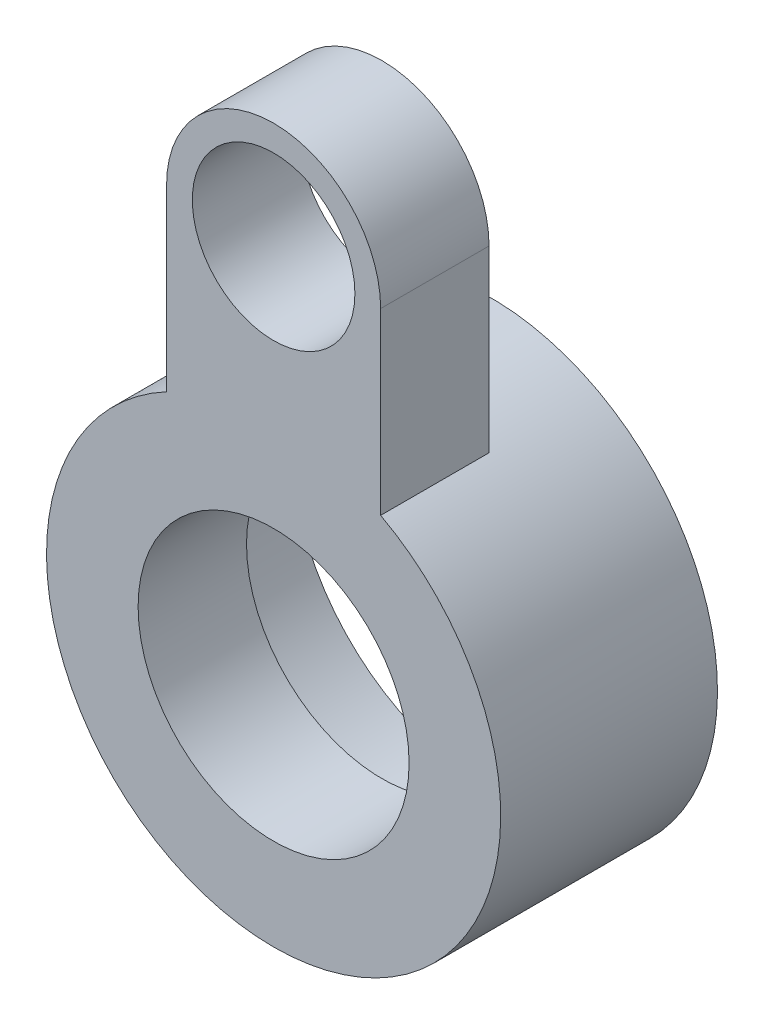
SolidWorks part; units mm, degrees
ref_plane "Front Plane" through (0, 0, 0) normal (0, 0, 1) x (1, 0, 0)
ref_plane "Top Plane" through (0, 0, 0) normal (0, 1, 0) x (1, 0, 0)
ref_plane "Right Plane" through (0, 0, 0) normal (1, 0, 0) x (0, 0, -1)
sketch "Sketch1" plane through (0, 0, 0) normal (0, 0, 1) x (1, 0, 0)
  circle A0 centre (0, 0) radius 10
  circle A1 centre (0, 7) radius 1.5
  circle A2 centre (0, 0) radius 2.5
  dimension "D2" = 20
  dimension "D3" = 3
  dimension "D4" = 5
  dimension "D1" = 7
extrude "Boss-Extrude1" add sketch "Sketch1" along normal blind 2
sketch "Sketch2" plane through (0, 0, 2) normal (0, 0, 1) x (1, 0, 0)
  line L0 (0, 8.975) -> (0, -8.975) construction
  line L1 (0, 0) -> (-10, 0) construction
  line L2 (-1.975, 7) -> (-1.975, 3.6953)
  line L3 (1.975, 7) -> (1.975, 3.6953)
  arc A0 (1.975, 3.6953) -> (4.19, 0) centre (0, 0) cw
  arc A1 (1.975, 7) -> (-1.975, 7) centre (0, 7) ccw
  circle A2 centre (0, 0) radius 10 construction
  arc A3 (-1.975, 3.6953) -> (-4.19, 0) centre (0, 0) ccw
  arc A4 (-4.19, 0) -> (4.19, 0) centre (0, 0) ccw
  circle A6 centre (0, 0) radius 10
  circle A7 centre (0, 0) radius 10
  point P2 (0, 0)
  dimension "D2" = 8.38
  dimension "D1" = 0
extrude "Cut-Extrude1" cut sketch "Sketch2" against normal blind 10
sketch "Sketch3" [suppressed] plane through (0, 0, 2) normal (0, 0, 1) x (1, 0, 0)
  line L0 (10.4381, 0) -> (0, 0) construction
  line L1 (1.975, 3.6953) -> (1.975, 7) construction
  line L2 (-1.975, 7) -> (-1.975, 3.6953) construction
  line L3 (1.975, 3.6953) -> (1.975, 7) construction
  line L4 (-1.975, 7) -> (-1.975, 3.6953) construction
  line L5 (-1.975, -7) -> (-1.975, -3.6953)
  line L6 (1.975, -3.6953) -> (1.975, -7)
  line L7 (-1.975, -3.6953) -> (1.975, -3.6953)
  arc A0 (1.975, 7) -> (-1.975, 7) centre (0, 7) ccw construction
  circle A1 centre (0, 7) radius 1.5 construction
  arc A2 (1.975, 7) -> (-1.975, 7) centre (0, 7) ccw construction
  circle A3 centre (0, 7) radius 1.5 construction
  circle A4 centre (0, -7) radius 1.5
  arc A5 (1.975, -7) -> (-1.975, -7) centre (0, -7) cw
extrude "Boss-Extrude2" [suppressed] add sketch "Sketch3" against normal up to vertex
sketch "Sketch4" plane through (0, 0, 0) normal (0, 0, -1) x (-1, 0, 0)
  circle A0 centre (0, 0) radius 4.19
  circle A1 centre (0, 0) radius 3.6671
  arc A2 (-1.975, 3.6953) -> (1.975, 3.6953) centre (0, 0) ccw construction
extrude "Boss-Extrude3" add sketch "Sketch4" along normal blind 2
sketch "Sketch5" plane through (0, 0, 2) normal (0, 0, 1) x (1, 0, 0)
  line L0 (0, 7) -> (0, 0)
